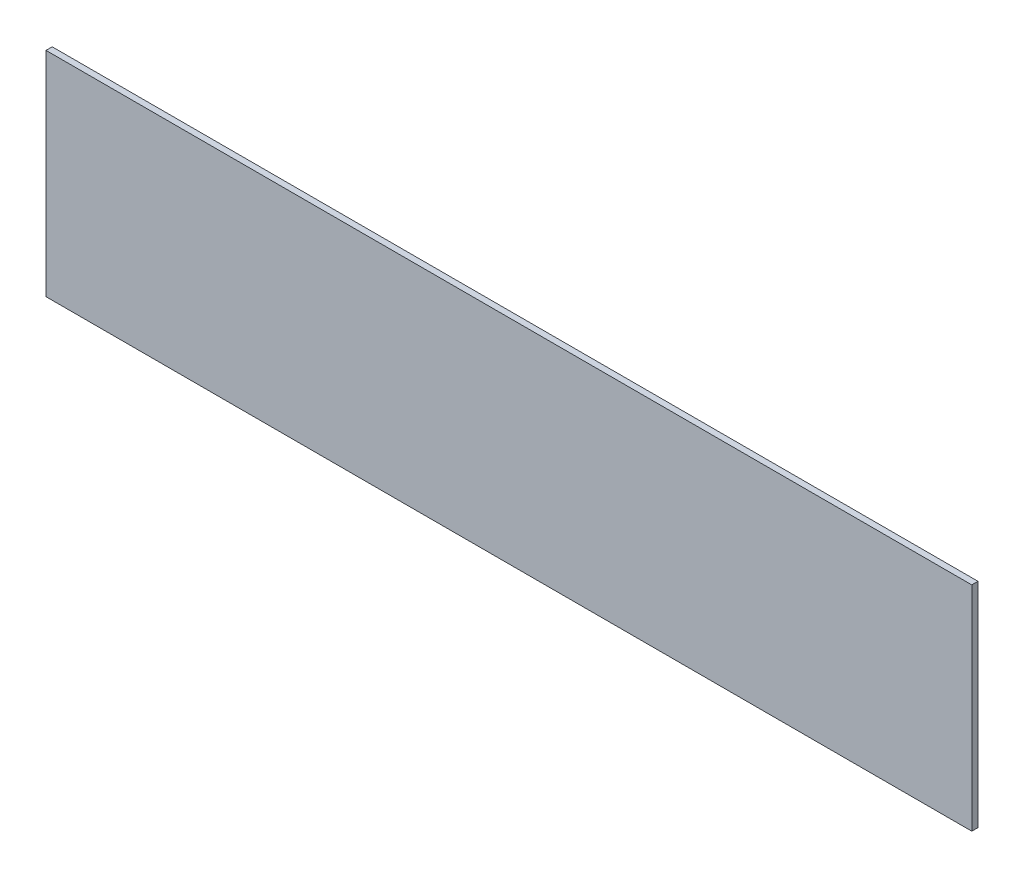
SolidWorks part; units mm, degrees
ref_plane "Front Plane" through (0, 0, 0) normal (0, 0, 1) x (1, 0, 0)
ref_plane "Top Plane" through (0, 0, 0) normal (0, 1, 0) x (1, 0, 0)
ref_plane "Right Plane" through (0, 0, 0) normal (1, 0, 0) x (0, 0, -1)
sketch "Sketch1" plane through (0, 0, 0) normal (0, 0, 1) x (1, 0, 0)
  line L1 (0, 0) -> (450, 0)
  line L2 (0, 0) -> (0, 103)
  line L3 (0, 103) -> (450, 103)
  line L4 (450, 0) -> (450, 103)
  dimension "D1" = 450
  dimension "D2" = 103
extrude "Boss-Extrude1" add sketch "Sketch1" along normal blind 3
sketch "Sketch7" plane through (0, 0, 0) normal (0, 0, -1) x (-1, 0, 0)
  line L0 (0, 0) -> (-450, 0) construction
  line L1 (0, 103) -> (-3, 103)
  line L2 (0, 103) -> (0, 0)
  line L3 (0, 0) -> (-3, 0)
  line L4 (-3, 103) -> (-3, 0)
  dimension "D1" = 3
extrude "Cut-Extrude5" cut sketch "Sketch7" against normal blind 10
